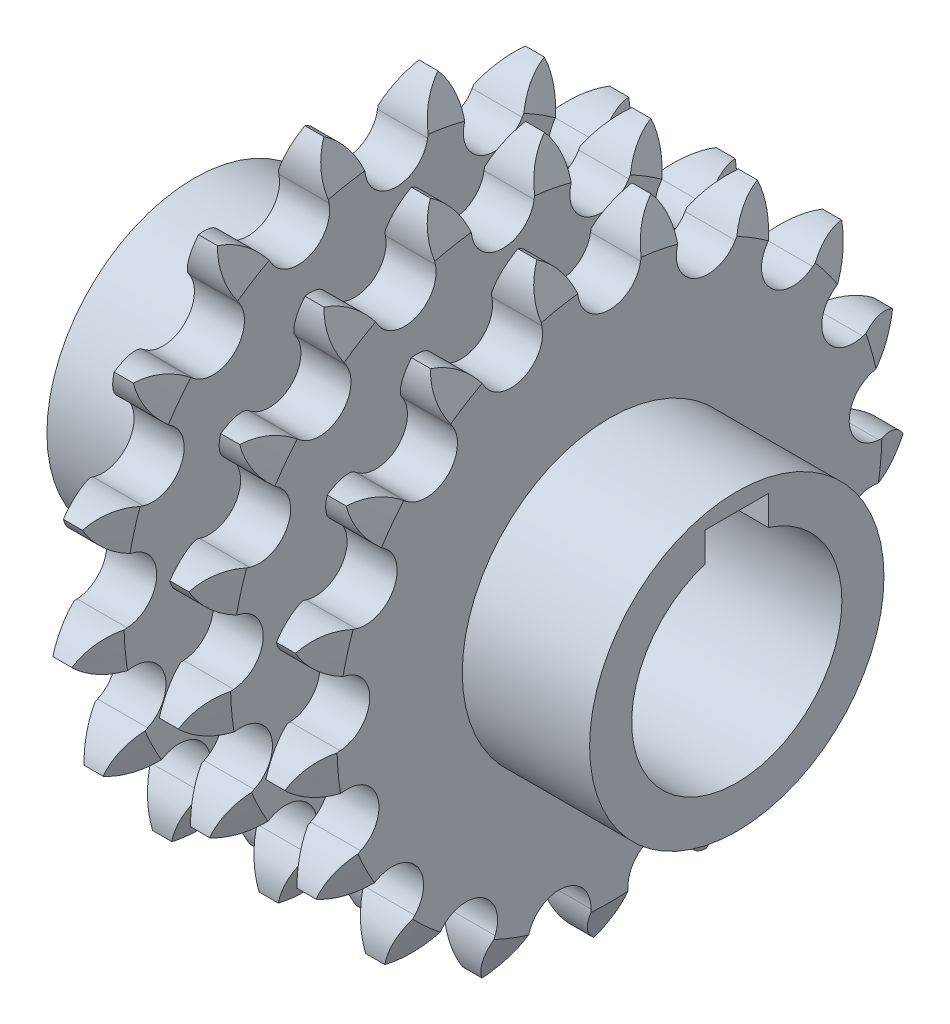
SolidWorks part; units mm, degrees
ref_plane "Front Plane" through (0, 0, 0) normal (0, 0, 1) x (1, 0, 0)
ref_plane "Top Plane" through (0, 0, 0) normal (0, 1, 0) x (1, 0, 0)
ref_plane "Right Plane" through (0, 0, 0) normal (1, 0, 0) x (0, 0, -1)
sketch "Sketch1" plane through (0, 0, 0) normal (0, 0, 1) x (1, 0, 0)
  line L0 (-2.38, 0) -> (2.38, 0)
  line L1 (2.38, 0) -> (2.38, 25.915)
  line L2 (2.38, 25.915) -> (0.75, 29.915)
  line L3 (0.75, 29.915) -> (-0.75, 29.915)
  line L4 (-0.75, 29.915) -> (-2.38, 25.915)
  line L5 (-2.38, 25.915) -> (-2.38, 0)
  line L6 (-2.38, 25.915) -> (2.38, 25.915) construction
  line L7 (0, 29.915) -> (0, 25.915) construction
  point P4 (0, 0)
  dimension "D1" = 4.76
  dimension "D2" = 25.915
  dimension "D3" = 4
  dimension "D4" = 1.5
revolve "Revolve1" add sketch "Sketch1" angle 360 about L0
sketch "Sketch2" plane through (2.38, 0, 0) normal (1, 0, 0) x (0, 0, -1)
  line L0 (0, 25.915) -> (0, 22.915) construction
  circle A0 centre (0, 0) radius 25.915 construction
  arc A1 (-2.964, 25.4519) -> (2.964, 25.4519) centre (0, 25.915) ccw
  arc A2 (-2.964, 25.4519) -> (-5.4252, 29.0224) centre (-7.9041, 24.6802) ccw
  arc A3 (2.964, 25.4519) -> (5.4252, 29.0224) centre (7.9041, 24.6802) cw
  circle A4 centre (0, 0) radius 29.915 construction
  arc A7 (6.4304, 24.804) -> (5.4252, 29.0224) centre (1.5451, 25.8689) ccw
  arc A8 (6.4304, 24.804) -> (11.9582, 22.6625) centre (9.3616, 24.165) ccw
  arc A9 (11.9582, 22.6625) -> (15.543, 25.1028) centre (16.2859, 20.1583) cw
  arc A11 (14.9564, 20.8061) -> (15.543, 25.1028) centre (10.7857, 23.5639) ccw
  arc A12 (14.9564, 20.8061) -> (19.3373, 16.8123) centre (17.4588, 19.1514) ccw
  arc A13 (19.3373, 16.8123) -> (23.5616, 17.7929) centre (22.4682, 12.9139) cw
  arc A15 (21.4625, 13.9982) -> (23.5616, 17.7929) centre (18.5696, 18.0764) ccw
  arc A16 (21.4625, 13.9982) -> (24.1048, 8.6916) centre (23.1982, 11.5513) ccw
  arc A17 (24.1048, 8.6916) -> (28.3981, 8.0799) centre (25.616, 3.9254) cw
  arc A19 (25.0699, 5.2998) -> (28.3981, 8.0799) centre (23.8456, 10.1476) ccw
  arc A20 (25.0699, 5.2998) -> (25.6169, -0.603) centre (25.8045, 2.3911) ccw
  arc A21 (25.6169, -0.603) -> (29.3992, -2.7242) centre (25.3042, -5.5932) cw
  arc A23 (25.2915, -4.1144) -> (29.3992, -2.7242) centre (25.9011, 0.8483) ccw
  arc A24 (25.2915, -4.1144) -> (23.6692, -9.8162) centre (24.9257, -7.092) ccw
  arc A25 (23.6692, -9.8162) -> (26.4298, -13.1605) centre (21.575, -14.3564) cw
  arc A27 (22.0973, -12.9729) -> (26.4298, -13.1605) centre (24.4585, -8.5655) ccw
  arc A28 (22.0973, -12.9729) -> (18.5249, -17.7036) centre (20.6806, -15.6173) ccw
  arc A29 (18.5249, -17.7036) -> (19.891, -21.8194) centre (14.9319, -21.1808) cw
  arc A31 (15.9188, -20.0793) -> (19.891, -21.8194) centre (19.7127, -16.8225) ccw
  arc A32 (15.9188, -20.0793) -> (10.8786, -23.2001) centre (13.6425, -22.0334) ccw
  arc A33 (10.8786, -23.2001) -> (10.6657, -27.5314) centre (6.2722, -25.1445) cw
  arc A35 (7.5904, -24.4739) -> (10.6657, -27.5314) centre (12.3045, -22.8076) ccw
  arc A36 (7.5904, -24.4739) -> (1.7632, -25.5632) centre (4.7619, -25.4737) ccw
  arc A37 (1.7632, -25.5632) -> (0, -29.5252) centre (-3.2346, -25.7123) cw
  arc A39 (-1.7632, -25.5632) -> (0, -29.5252) centre (3.2346, -25.7123) ccw
  arc A40 (-1.7632, -25.5632) -> (-7.5904, -24.4739) centre (-4.7619, -25.4737) ccw
  arc A41 (-7.5904, -24.4739) -> (-10.6657, -27.5314) centre (-12.3045, -22.8076) cw
  arc A43 (-10.8786, -23.2001) -> (-10.6657, -27.5314) centre (-6.2722, -25.1445) ccw
  arc A44 (-10.8786, -23.2001) -> (-15.9188, -20.0793) centre (-13.6425, -22.0334) ccw
  arc A45 (-15.9188, -20.0793) -> (-19.891, -21.8194) centre (-19.7127, -16.8225) cw
  arc A47 (-18.5249, -17.7036) -> (-19.891, -21.8194) centre (-14.9319, -21.1808) ccw
  arc A48 (-18.5249, -17.7036) -> (-22.0973, -12.9729) centre (-20.6806, -15.6173) ccw
  arc A49 (-22.0973, -12.9729) -> (-26.4298, -13.1605) centre (-24.4585, -8.5655) cw
  arc A51 (-23.6692, -9.8162) -> (-26.4298, -13.1605) centre (-21.575, -14.3564) ccw
  arc A52 (-23.6692, -9.8162) -> (-25.2915, -4.1144) centre (-24.9257, -7.092) ccw
  arc A53 (-25.2915, -4.1144) -> (-29.3992, -2.7242) centre (-25.9011, 0.8483) cw
  arc A55 (-25.6169, -0.603) -> (-29.3992, -2.7242) centre (-25.3042, -5.5932) ccw
  arc A56 (-25.6169, -0.603) -> (-25.0699, 5.2998) centre (-25.8045, 2.3911) ccw
  arc A57 (-25.0699, 5.2998) -> (-28.3981, 8.0799) centre (-23.8456, 10.1476) cw
  arc A59 (-24.1048, 8.6916) -> (-28.3981, 8.0799) centre (-25.616, 3.9254) ccw
  arc A60 (-24.1048, 8.6916) -> (-21.4625, 13.9982) centre (-23.1982, 11.5513) ccw
  arc A61 (-21.4625, 13.9982) -> (-23.5616, 17.7929) centre (-18.5696, 18.0764) cw
  arc A63 (-19.3373, 16.8123) -> (-23.5616, 17.7929) centre (-22.4682, 12.9139) ccw
  arc A64 (-19.3373, 16.8123) -> (-14.9564, 20.8061) centre (-17.4588, 19.1514) ccw
  arc A65 (-14.9564, 20.8061) -> (-15.543, 25.1028) centre (-10.7857, 23.5639) cw
  arc A67 (-11.9582, 22.6625) -> (-15.543, 25.1028) centre (-16.2859, 20.1583) ccw
  arc A68 (-11.9582, 22.6625) -> (-6.4304, 24.804) centre (-9.3616, 24.165) ccw
  arc A69 (-6.4304, 24.804) -> (-5.4252, 29.0224) centre (-1.5451, 25.8689) cw
  circle A74 centre (0, 0) radius 29.915
  point P127 (0, 0)
  dimension "D1" = 6
  dimension "D2" = 10
  dimension "D3" = 17
extrude "Cut-Extrude1" cut sketch "Sketch2" against normal through all
pattern_linear "LPattern4" count 3 spacing 10.13 along (1, 0, 0) of "Cut-Extrude1", "Revolve1"
sketch "Sketch4" plane through (-2.38, 0, 0) normal (-1, 0, 0) x (0, 0, 1)
  circle A0 centre (0, 0) radius 14
  dimension "D1" = 28
extrude "Boss-Extrude1" add sketch "Sketch4" along normal blind 14.49 and the other way blind 37.13
sketch "Sketch5" plane through (34.75, 0, 0) normal (1, 0, 0) x (0, 0, -1)
  circle A0 centre (0, 0) radius 10
  dimension "D1" = 20
extrude "Cut-Extrude2" cut sketch "Sketch5" against normal through all
sketch "Sketch6" plane through (34.75, 0, 0) normal (1, 0, 0) x (0, 0, -1)
  line L0 (0, 0) -> (0, 10) construction
  line L1 (-3, 12.3394) -> (3, 12.3394)
  line L2 (-3, 12.3394) -> (-3, 9.5394)
  line L3 (-3, 9.5394) -> (3, 9.5394)
  line L4 (3, 12.3394) -> (3, 9.5394)
  circle A1 centre (0, 0) radius 10 construction
  point P4 (-2.2705, 9.6707)
  point P5 (0, 0)
  point P9 (-2.2987, 11.8027)
  point P12 (-2.2607, 9.7411)
  point P13 (-2.0695, 12.5835)
  dimension "D1" = 2.8
  dimension "D2" = 6
extrude "Cut-Extrude3" cut sketch "Sketch6" against normal blind 8
